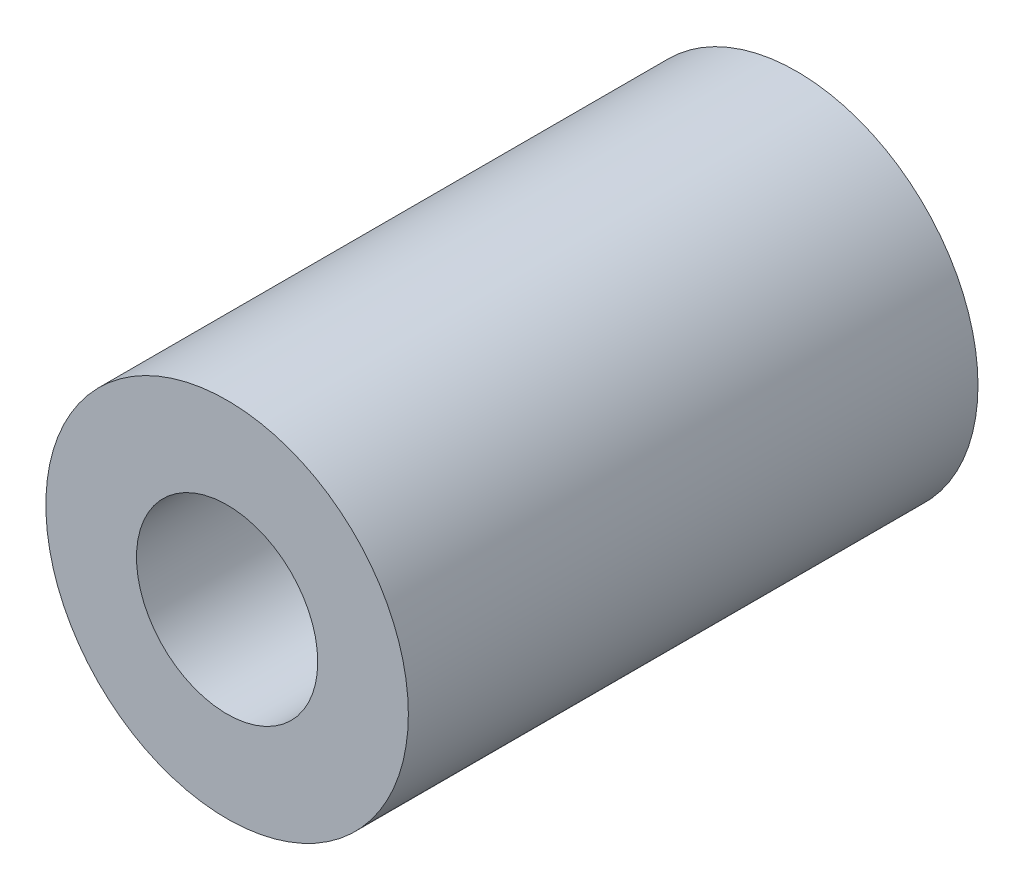
SolidWorks part; units mm, degrees
ref_plane "前视基准面" through (0, 0, 0) normal (0, 0, 1) x (1, 0, 0)
ref_plane "上视基准面" through (0, 0, 0) normal (0, 1, 0) x (1, 0, 0)
ref_plane "右视基准面" through (0, 0, 0) normal (1, 0, 0) x (0, 0, -1)
sketch "草图1" plane through (0, 0, 0) normal (0, 0, 1) x (1, 0, 0)
  circle A0 centre (0, 0) radius 7
  dimension "D1" = 14
extrude "凸台-拉伸1" add sketch "草图1" along normal blind 22
sketch "草图2" plane through (0, 0, 22) normal (0, 0, 1) x (1, 0, 0)
  circle A0 centre (0, 0) radius 3
  dimension "D1" = 6
extrude "切除-拉伸1" cut sketch "草图2" against normal through all
sketch "草图3" plane through (0, 0, 22) normal (0, 0, 1) x (1, 0, 0)
  circle A0 centre (0, 0) radius 3.5
  dimension "D1" = 7
extrude "切除-拉伸2" cut sketch "草图3" against normal blind 7
